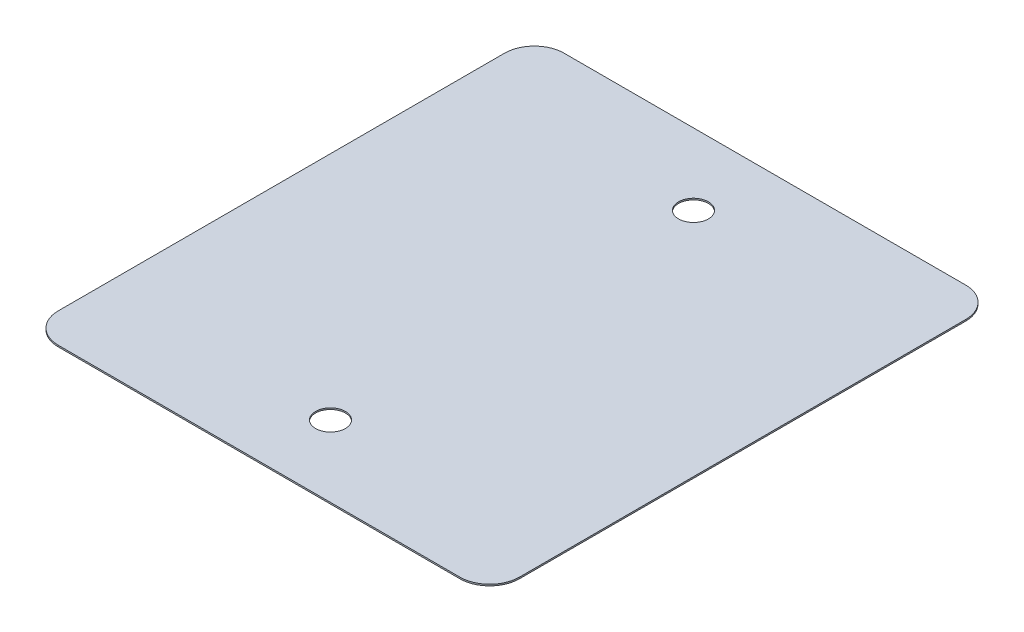
SolidWorks part; units mm, degrees
ref_plane "Front Plane" through (0, 0, 0) normal (0, 0, 1) x (1, 0, 0)
ref_plane "Top Plane" through (0, 0, 0) normal (0, 1, 0) x (1, 0, 0)
ref_plane "Right Plane" through (0, 0, 0) normal (1, 0, 0) x (0, 0, -1)
sketch "Sketch1" plane through (0, 0, 0) normal (0, 1, 0) x (1, 0, 0)
  line L0 (-7.75, 8.5) -> (7.75, -8.5) construction
  line L1 (-7.75, 8.5) -> (7.75, 8.5)
  line L2 (-7.75, 8.5) -> (-7.75, -8.5)
  line L3 (-7.75, -8.5) -> (7.75, -8.5)
  line L4 (7.75, 8.5) -> (7.75, -8.5)
  point P4 (0, 0)
  dimension "D1" = 15.5
  dimension "D2" = 17
extrude "Boss-Extrude1" add sketch "Sketch1" along normal blind 0.05
fillet "Fillet1" radius 1 4 edges at (7.75, 0.025, -8.5) (-7.75, 0.025, -8.5) (-7.75, 0.025, 8.5) (7.75, 0.025, 8.5)
sketch "Sketch2" plane through (0, 0.05, 0) normal (0, 1, 0) x (1, 0, 0)
  line L0 (0, 0) -> (3.7079, 0) construction
  line L1 (0, 0) -> (0, 4.463) construction
  circle A0 centre (0, 6.1) radius 0.5
  circle A1 centre (0, -6.1) radius 0.5
  dimension "D2" = 1
  dimension "D1" = 12.2
extrude "Cut-Extrude1" cut sketch "Sketch2" against normal through all
